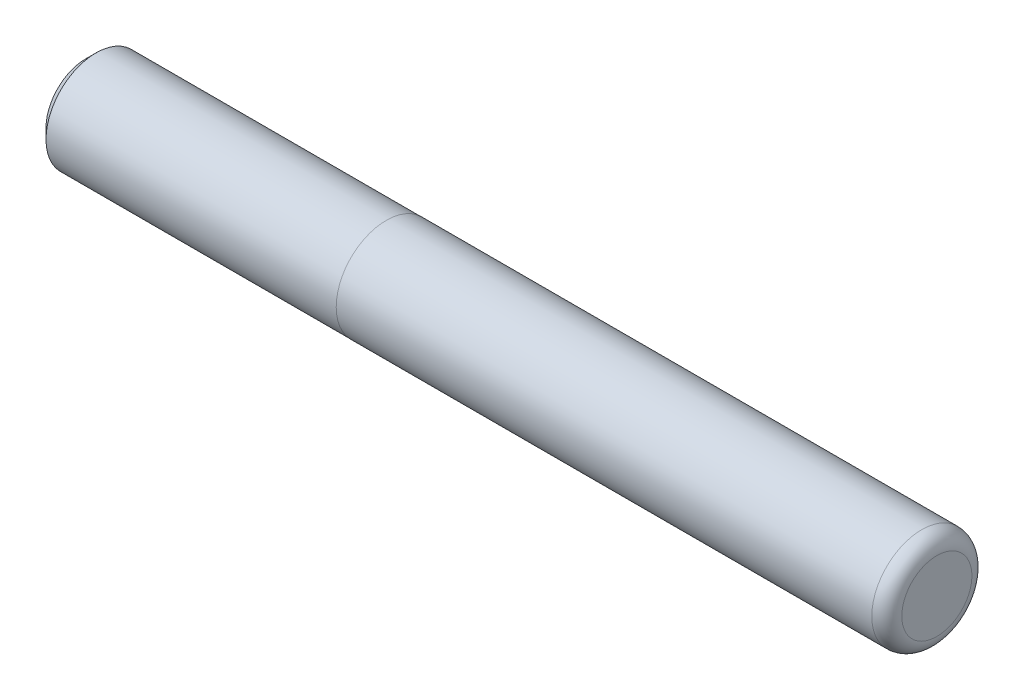
SolidWorks part; units mm, degrees
material "Stub"
ref_plane "Face" through (0, 0, 0) normal (0, 0, 1) x (1, 0, 0)
ref_plane "Dessus" through (0, 0, 0) normal (0, 1, 0) x (1, 0, 0)
ref_plane "Droite" through (0, 0, 0) normal (1, 0, 0) x (0, 0, -1)
sketch "Esquisse1" plane through (0, 0, 0) normal (0, 0, 1) x (1, 0, 0)
  line L0 (0, 0) -> (0, 3.5)
  line L1 (-1.5, 5) -> (-55, 5)
  line L2 (-55, 5) -> (-55, 4.99)
  line L3 (-55, 4.99) -> (-84, 4.99)
  line L4 (-85, 3.99) -> (-85, 0)
  line L5 (-85, 0) -> (0, 0)
  line L6 (0, 0) -> (-0.0066, -0.0902)
  line L7 (-84, 4.99) -> (-85, 3.99)
  arc A0 (0, 3.5) -> (-1.5, 5) centre (-1.5, 3.5) ccw
  point P6 (-85, 4.99)
  point P10 (0, 5)
  dimension "D5" = 1.5
  dimension "D1" = 55
  dimension "D2" = 5
  dimension "D3" = 4.99
  dimension "D4" = 30
revolve "Révolution1" add sketch "Esquisse1" angle 360 about L5
cosmetic thread "Représentation de filetage1" parameters "D2"=6.619
